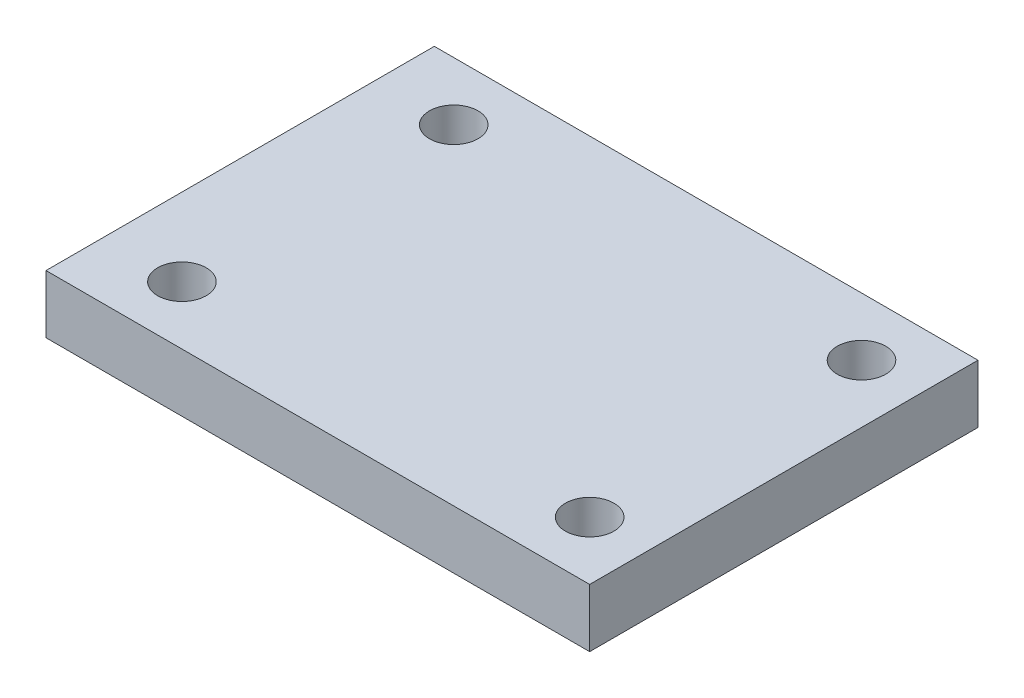
SolidWorks part; units mm, degrees
ref_plane "Front Plane" through (0, 0, 0) normal (0, 0, 1) x (1, 0, 0)
ref_plane "Top Plane" through (0, 0, 0) normal (0, 1, 0) x (1, 0, 0)
ref_plane "Right Plane" through (0, 0, 0) normal (1, 0, 0) x (0, 0, -1)
sketch "Sketch1" plane through (0, 0, 0) normal (0, 1, 0) x (1, 0, 0)
  line L0 (-14, 10) -> (14, 10)
  line L1 (14, -10) -> (-14, -10)
  line L2 (14, -10) -> (14, 10)
  line L4 (-14, -10) -> (-14, 10)
  line L5 (14, -10) -> (-14, 10) construction
  line L6 (14, 10) -> (-14, -10) construction
  circle A0 centre (-10, 7) radius 1.6945
  circle A1 centre (-10, -7) radius 2.2709
  circle A2 centre (11, -7) radius 2.2709
  circle A3 centre (11, 7) radius 2.9997
  point P0 (0, 0)
  dimension "D1" = 20
  dimension "D2" = 28
  dimension "D3" = 3
  dimension "D4" = 3
  dimension "D5" = 14
  dimension "D6" = 21
extrude "Boss-Extrude1" add sketch "Sketch1" along normal blind 3
hole_wizard "M3 Tapped Hole1" positions "Sketch4" profile "Sketch5" tap size "M3" standard "ISO" end condition through all
sketch "Sketch4" plane through (0, 0, 0) normal (0, -1, 0) x (-1, 0, 0)
  point P0 (-11, 7)
  point P3 (10, 7)
  point P6 (10, -7)
  point P9 (-11, -7)
sketch "Sketch5" plane through (11, 0, -7) normal (1, 0, 0) x (0, 0, -1)
  line L0 (0, 0) -> (0, 3)
  line L1 (0, 3) -> (1.25, 3)
  line L2 (1.25, 3) -> (1.25, 0)
  line L5 (1.25, 0) -> (0, 0)
  line L11 (0, -6.35) -> (0, 107.95) construction
  dimension "Thru Tap Drill Dia." = 2.5
  dimension "Thru Tap Drill Depth" = 3
cosmetic thread "Hole Thread1" parameters "D2"=3
cosmetic thread "Hole Thread2" parameters "D2"=3
cosmetic thread "Hole Thread3" parameters "D2"=3
cosmetic thread "Hole Thread4" parameters "D2"=3
